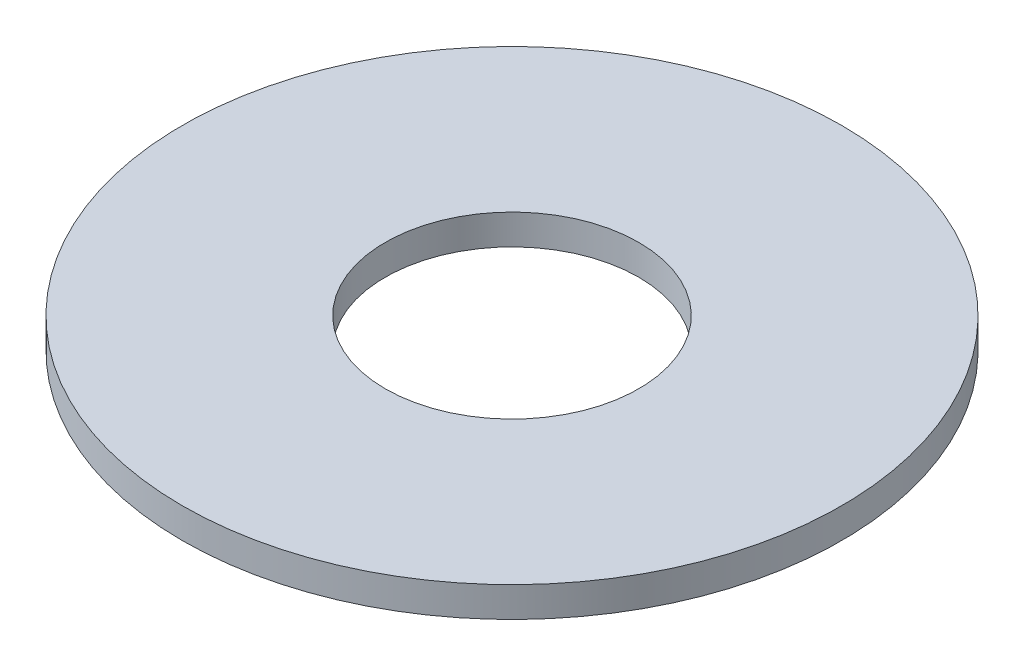
SolidWorks part; units mm, degrees
material "Acrylic (Medium-high impact)"
ref_plane "Front Plane" through (0, 0, 0) normal (0, 0, 1) x (1, 0, 0)
ref_plane "Top Plane" through (0, 0, 0) normal (0, 1, 0) x (1, 0, 0)
ref_plane "Right Plane" through (0, 0, 0) normal (1, 0, 0) x (0, 0, -1)
sketch "Sketch1" plane through (0, 0, 0) normal (0, 1, 0) x (1, 0, 0)
  circle A0 centre (0, 0) radius 34.6583
  circle A1 centre (0, 0) radius 13.335
  dimension "D1" = 69.3166
  dimension "D2" = 26.67
extrude "Boss-Extrude1" add sketch "Sketch1" along normal blind 3.175
